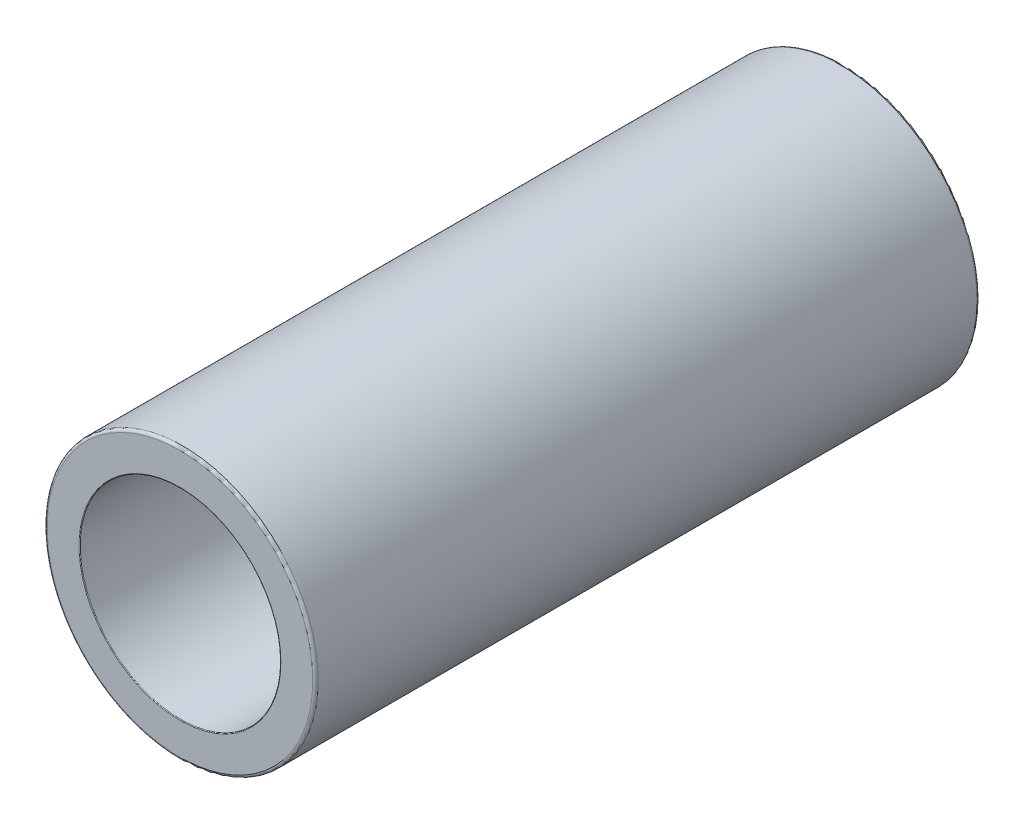
SolidWorks part; units mm, degrees
ref_plane "Piano frontale" through (0, 0, 0) normal (0, 0, 1) x (1, 0, 0)
ref_plane "Piano superiore" through (0, 0, 0) normal (0, 1, 0) x (1, 0, 0)
ref_plane "Piano destro" through (0, 0, 0) normal (1, 0, 0) x (0, 0, -1)
sketch "Schizzo1" plane through (0, 0, 0) normal (0, 0, 1) x (1, 0, 0)
  circle A0 centre (0, 0) radius 10
  circle A1 centre (0, 0) radius 7.4
extrude "Estrusione-Estrusione1" add sketch "Schizzo1" along normal blind 49
fillet "Raccordo1" radius 0.2 2 edges at (10, 0, 0) (10, 0, 49)
fillet "Raccordo2" radius 0.05 2 edges at (7.4, 0, 0) (7.4, 0, 49)
